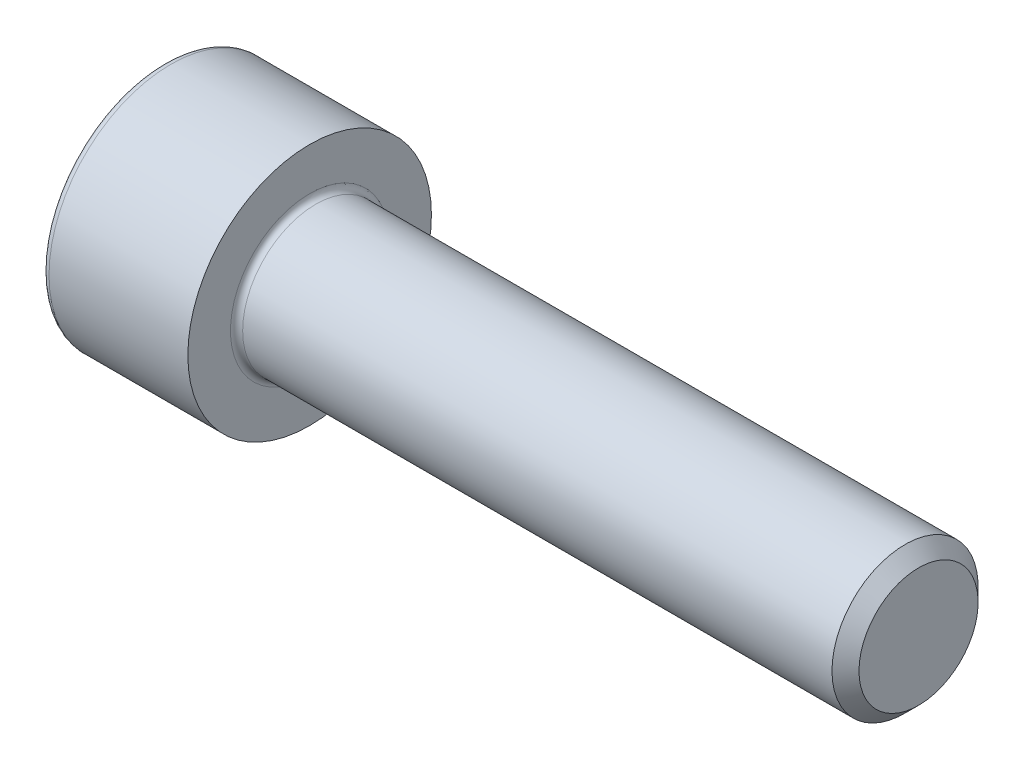
SolidWorks part; units mm, degrees
ref_plane "Plane1" through (0, 0, 0) normal (0, 0, 1) x (1, 0, 0)
ref_plane "Plane2" through (0, 0, 0) normal (0, 1, 0) x (1, 0, 0)
ref_plane "Plane3" through (0, 0, 0) normal (1, 0, 0) x (0, 0, -1)
sketch "BodySke" plane through (0, 0, 0) normal (0, 0, 1) x (1, 0, 0)
  line L0 (0, 0) -> (0, 5)
  line L1 (0, 5) -> (6, 5)
  line L2 (6, 5) -> (6, 3)
  line L3 (6, 3) -> (30.4455, 3)
  line L4 (31, 2.4455) -> (31, 0)
  line L5 (31, 0) -> (0, 0)
  line L6 (-31.75, 0) -> (127, 0) construction
  line L8 (31, 2.4455) -> (30.4455, 3)
  line L10 (31, -2.4455) -> (30.4455, -3) construction
  line L11 (7, 9.525) -> (7, 3.175) construction
  line L12 (6, 9.525) -> (6, 3.175) construction
  line L13 (-29, 9.525) -> (-29, 3.175) construction
  dimension "Diameter" = 6
  dimension "Head_ht" = 6
  dimension "Length" = 25
  dimension "Body_ch_ang" = 45
  dimension "Head_dia" = 10
  dimension "Minor_dia" = 4.891
  dimension "Advance" = 1
  dimension "Thread_nom" = 25
  dimension "Thread_length" = 60
revolve "Base-Revolve" add sketch "BodySke"
cosmetic thread "ThreadCosmetic"
fillet "Fillet1" radius 0.25 1 edges at (6, 0, 3)
fillet "Fillet2" radius 0.3 1 edges at (0, 0, 5)
sketch "Sketch2" plane through (0, 0, 0) normal (0, 0, 1) x (1, 0, 0)
  line L0 (0, 2.542) -> (3, 2.542)
  line L1 (3, 2.542) -> (4.4676, 0)
  line L2 (-31.75, 0) -> (127, 0) construction
  line L3 (4.4676, 0) -> (0, 0)
  line L4 (0, 0) -> (0, 2.542)
  line L6 (0, 0) -> (47.625, 0) construction
  dimension "D1" = 2.542
  dimension "D2" = 60
  dimension "Depth" = 3
revolve "Hex-PreBroach" cut sketch "Sketch2" angle 360 about L6
sketch "Sketch3" plane through (0, 0, 0) normal (-1, 0, 0) x (0, 0.5, 0.866)
  line L0 (1.4676, 2.542) -> (-1.4676, 2.542)
  line L1 (-1.4676, 2.542) -> (-2.9352, 0)
  line L2 (1.4676, 2.542) -> (2.9352, 0)
  line L3 (1.4676, -2.542) -> (2.9352, 0)
  line L4 (1.4676, -2.542) -> (-1.4676, -2.542)
  line L5 (-1.4676, -2.542) -> (-2.9352, 0)
  dimension "D1" = 2.542
  dimension "D2" = 2.542
  dimension "Hex_size" = 5.084
extrude "Hex" cut sketch "Sketch3" against normal blind 3
sketch "ThdSchSke" plane through (0, 0, 0) normal (0, 0, 1) x (1, 0, 0)
  line L0 (9, -2.4455) -> (8.6117, -3)
  line L1 (9, -2.4455) -> (9.3883, -3)
  line L2 (9.3883, -3) -> (9.3883, -3.75)
  line L3 (-3.175, 0) -> (5.1513, 0) construction
  line L4 (0, 4.7) -> (0, -4.7) construction
  line L5 (9.3883, -3.75) -> (8.6117, -3.75)
  line L6 (8.6117, -3.75) -> (8.6117, -3)
  dimension "Thread_minor" = 4.891
  dimension "Diameter" = 6
  dimension "Start" = 9
  dimension "SideAngle" = 55
  dimension "VeeAngle" = 70
  dimension "Overcut" = 7.5
revolve "ThreadSchematic" [suppressed] cut sketch "ThdSchSke" angle 360 about L3
pattern_linear "ThdSchPat" [suppressed]
equation "\"D2@Sketch3\" = \"Hex_size@Sketch3\" / 2"
equation "\"D1@Sketch3\" = \"Hex_size@Sketch3\" / 2"
equation "\"D1@Sketch2\" = \"Hex_size@Sketch3\" / 2"
equation "\"Thread_minor@ThreadCosmetic\"  =  \"Minor_dia@BodySke\""
equation "\"Depth@Sketch2\" =  \"Key_eng@Hex\""
equation "\"Thread_length@ThreadCosmetic\" = ((sgn( (\"Length@BodySke\" - \"Advance@BodySke\" * 3.0) - \"Thread_nom@BodySke\" )-1)*( (\"Length@BodySke\" - \"Advance@BodySke\" * 3.0) - \"Thread_nom@BodySke\" ))/-2+ \"Thread_nom@BodySke\""
equation "\"Thread_minor@ThdSchSke\" = \"Minor_dia@BodySke\""
equation "\"Diameter@ThdSchSke\" = \"Diameter@BodySke\""
equation "\"Overcut@ThdSchSke\" = \"Diameter@BodySke\" * 1.25"
equation "\"Start@ThdSchSke\" = \"Head_ht@BodySke\" + \"Length@BodySke\" - \"Thread_length@ThreadCosmetic\"  '---Non-countersunk---"
equation "\"Num_threads@ThdSchPat\" = int( \"Thread_length@ThreadCosmetic\" / \"Advance@BodySke\" + 0.999 )  + 1"
equation "\"Advance@ThdSchPat\" = \"Thread_length@ThreadCosmetic\" /  (\"Num_threads@ThdSchPat\" - 1) 'relax it"
equation "\"Num_threads@ThdSchPat\" = \"Num_threads@ThdSchPat\" - sgn( \"Num_threads@ThdSchPat\" - 1) '---chamfered tips only---"
